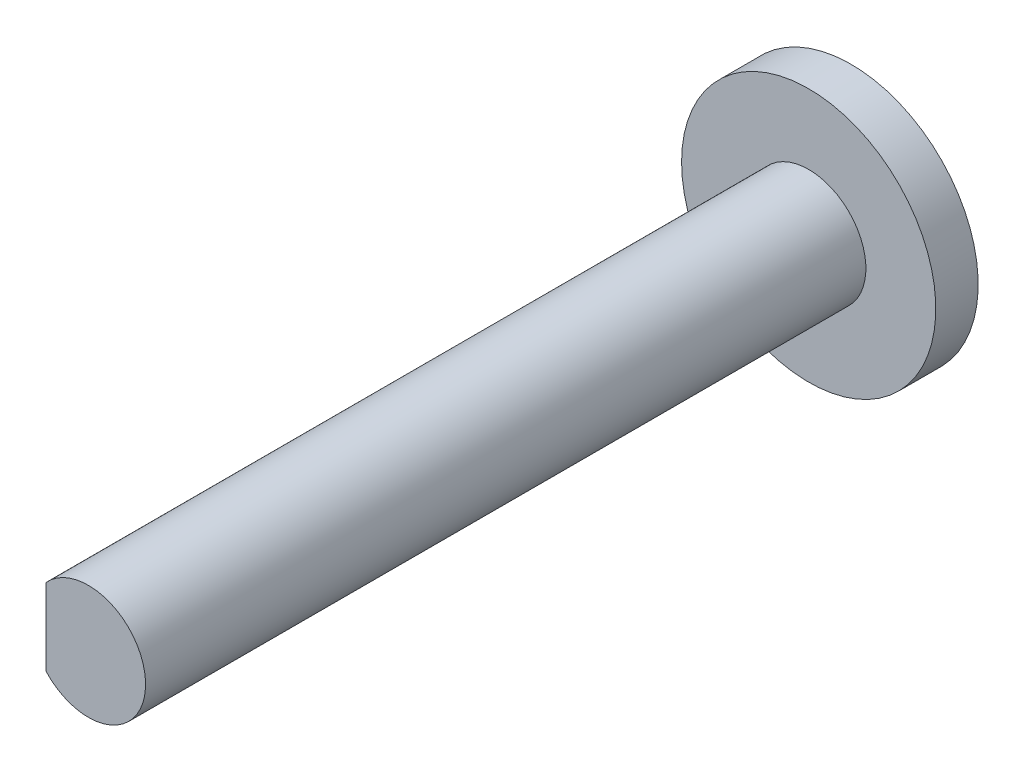
SolidWorks part; units mm, degrees
ref_plane "Front Plane" through (0, 0, 0) normal (0, 0, 1) x (1, 0, 0)
ref_plane "Top Plane" through (0, 0, 0) normal (0, 1, 0) x (1, 0, 0)
ref_plane "Right Plane" through (0, 0, 0) normal (1, 0, 0) x (0, 0, -1)
sketch "Sketch2" plane through (0, 0, 0) normal (0, 0, 1) x (1, 0, 0)
  circle A0 centre (0, 0) radius 1.35
  dimension "D1" = 2.7
extrude "Boss-Extrude1" add sketch "Sketch2" along normal mid plane 17
sketch "Sketch4" plane through (0, 0, -8.5) normal (0, 0, -1) x (-1, 0, 0)
  line L0 (1, 0.9069) -> (1, -0.9069)
  arc A0 (1, -0.9069) -> (1, 0.9069) centre (0, 0) ccw
  dimension "D2" = 2.7
  dimension "D1" = 1
extrude "Cut-Extrude1" cut sketch "Sketch4" against normal blind 6.4
sketch "Sketch5" plane through (0, 0, 8.5) normal (0, 0, 1) x (1, 0, 0)
  line L0 (-1, 0.9069) -> (-1, -0.9069)
  arc A0 (-1, 0.9069) -> (-1, -0.9069) centre (0, 0) ccw
  dimension "D2" = 1.35
  dimension "D1" = 1
extrude "Cut-Extrude2" cut sketch "Sketch5" against normal blind 3.2
sketch "Sketch6" plane through (0, 0, -8.5) normal (0, 0, -1) x (-1, 0, 0)
  circle A0 centre (0, 0) radius 3
  dimension "D1" = 6
extrude "Boss-Extrude2" add sketch "Sketch6" along normal blind 1 contours A0
